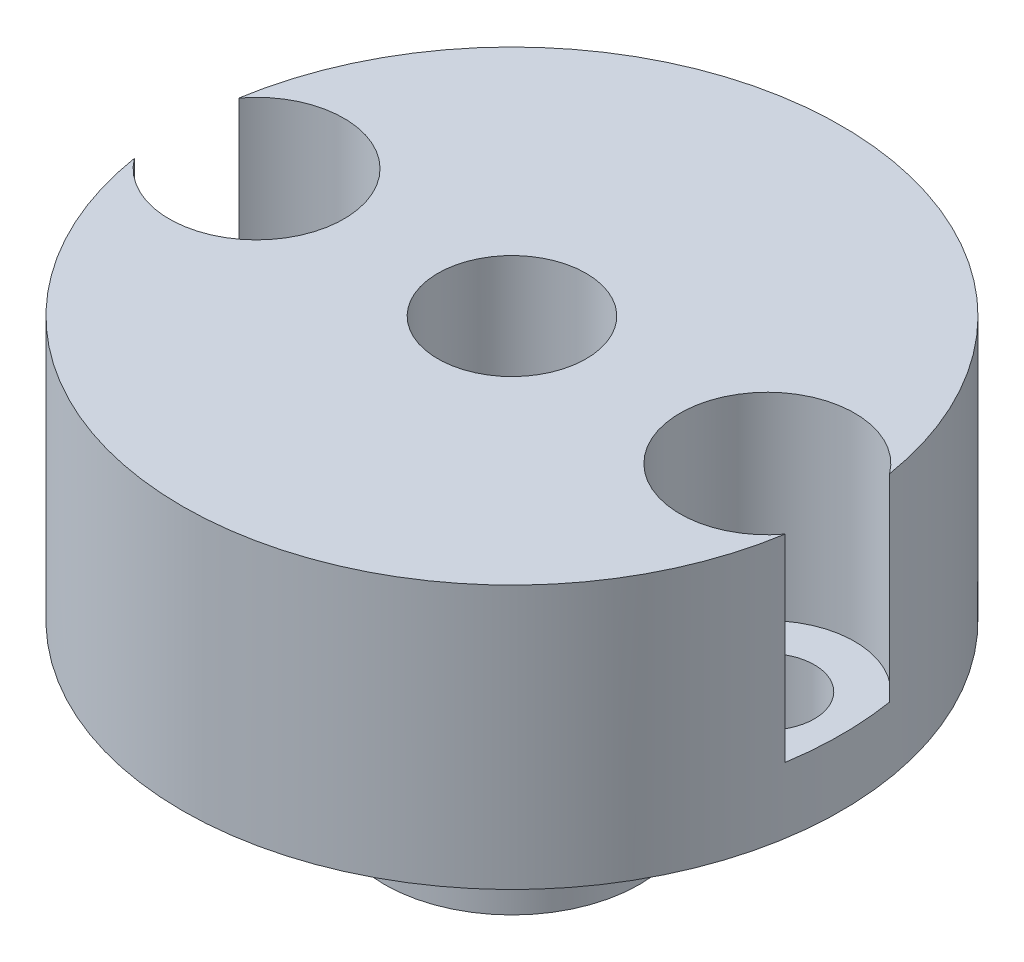
SolidWorks part; units mm, degrees
ref_plane "Front Plane" through (0, 0, 0) normal (0, 0, 1) x (1, 0, 0)
ref_plane "Top Plane" through (0, 0, 0) normal (0, 1, 0) x (1, 0, 0)
ref_plane "Right Plane" through (0, 0, 0) normal (1, 0, 0) x (0, 0, -1)
sketch "Sketch1" plane through (0, 0, 0) normal (0, 1, 0) x (1, 0, 0)
  circle A0 centre (0, 0) radius 3.875
  dimension "D1" = 7.75
extrude "Boss-Extrude1" add sketch "Sketch1" along normal blind 9 and the other way blind 4
sketch "Sketch2" plane through (0, 0, 0) normal (0, 1, 0) x (1, 0, 0)
  circle A0 centre (0, 0) radius 5.4
  dimension "D1" = 10.8
extrude "Boss-Extrude2" add sketch "Sketch2" along normal up to surface (9 mm away) up to face at (0, 9, 3.875)
sketch "Sketch7" plane through (0, 9, 0) normal (0, 1, 0) x (1, 0, 0)
  circle A0 centre (0, 0) radius 10
  dimension "D1" = 20
extrude "Boss-Extrude4" add sketch "Sketch7" against normal blind 8
sketch "Sketch3" plane through (0, 9, 0) normal (0, 1, 0) x (1, 0, 0)
  circle A0 centre (0, 0) radius 7.75 construction
  circle A1 centre (-7.75, 0) radius 1.425
  dimension "D1" = 15.5
  dimension "D2" = 2.85
extrude "Cut-Extrude2" cut sketch "Sketch3" against normal up to surface (9 mm away) and the other way through all up to face at (0, 0, 3.875)
sketch "Sketch6" plane through (0, 9, 0) normal (0, 1, 0) x (1, 0, 0)
  line L1 (-5.1, 0) -> (-6.425, 2.295) construction
  line L2 (-6.425, 2.295) -> (-9.075, 2.295) construction
  line L3 (-9.075, 2.295) -> (-10.4, 0) construction
  line L4 (-10.4, 0) -> (-9.075, -2.295) construction
  line L5 (-9.075, -2.295) -> (-6.425, -2.295) construction
  line L6 (-6.425, -2.295) -> (-5.1, 0) construction
  circle A1 centre (-7.75, 0) radius 2.65
  dimension "D1" = 5.3
extrude "Cut-Extrude3" cut sketch "Sketch6" against normal blind 6
pattern_circular "CirPattern1" count 2 over 360 about axis through (0, 0, 0) along (0, 1, 0) of "Cut-Extrude2", "Cut-Extrude3"
sketch "Sketch8" plane through (0, -4, 0) normal (0, -1, 0) x (1, 0, 0)
  circle A0 centre (0, 0) radius 2.25
  dimension "D1" = 4.5
extrude "Cut-Extrude4" cut sketch "Sketch8" against normal through all both and the other way through all
